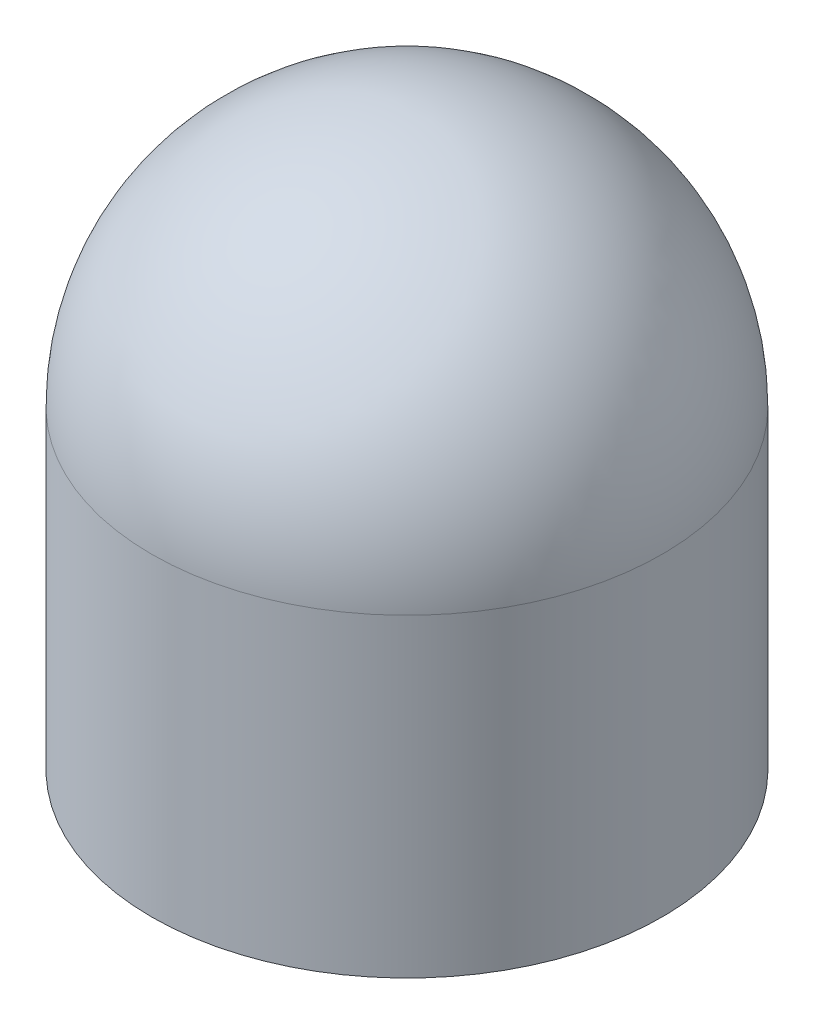
SolidWorks part; units mm, degrees
ref_plane "Front Plane" through (0, 0, 0) normal (0, 0, 1) x (1, 0, 0)
ref_plane "Top Plane" through (0, 0, 0) normal (0, 1, 0) x (1, 0, 0)
ref_plane "Right Plane" through (0, 0, 0) normal (1, 0, 0) x (0, 0, -1)
sketch "Sketch1" plane through (0, 0, 0) normal (0, 1, 0) x (1, 0, 0)
  circle A0 centre (0, 0) radius 165.1
  dimension "D1" = 330.2
extrude "Boss-Extrude1" add sketch "Sketch1" along normal blind 203.2
sketch "Sketch2" plane through (0, 203.2, 0) normal (0, 1, 0) x (1, 0, 0)
  line L0 (0, 165.1) -> (0, -165.1)
  arc A0 (0, -165.1) -> (0, 165.1) centre (0, 0) ccw
revolve "Revolve1" add sketch "Sketch2" angle 180 about L0
shell "Shell1" thickness 2.54
